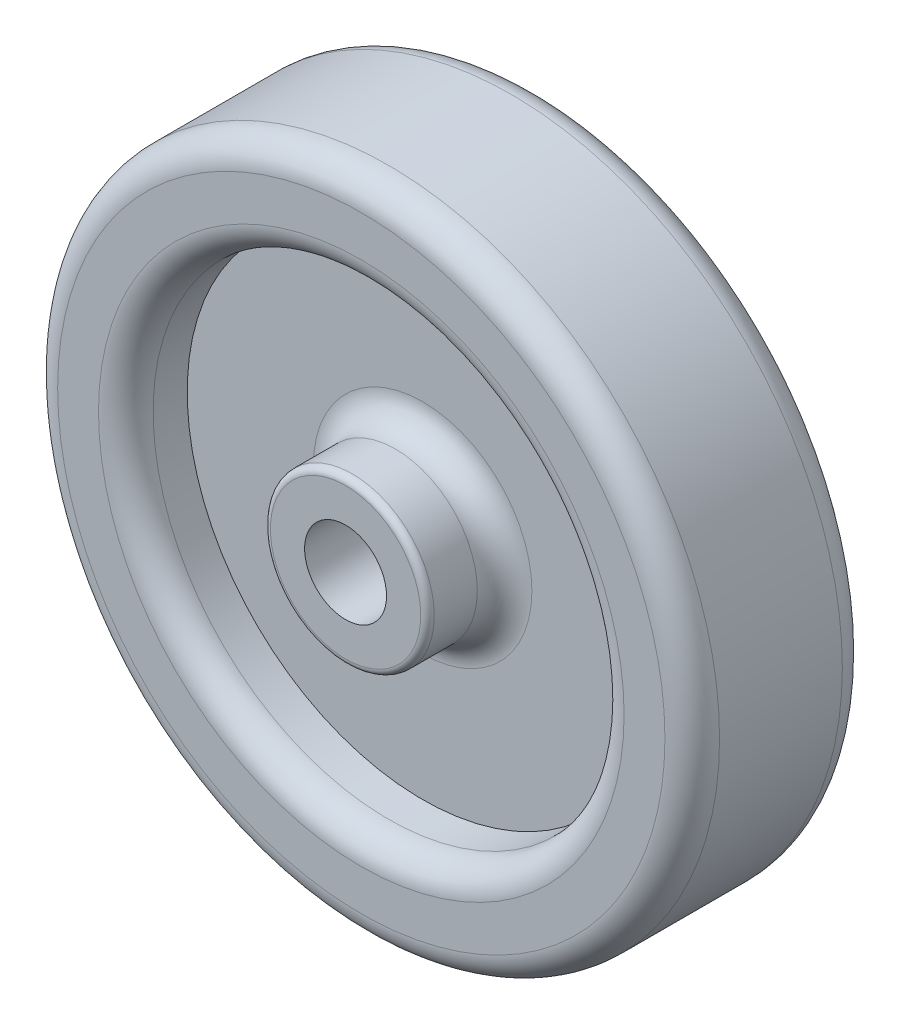
SolidWorks part; units mm, degrees
ref_plane "Front" through (0, 0, 0) normal (0, 0, 1) x (1, 0, 0)
ref_plane "Top" through (0, 0, 0) normal (0, 1, 0) x (1, 0, 0)
ref_plane "Right" through (0, 0, 0) normal (1, 0, 0) x (0, 0, -1)
sketch "Sketch1" plane through (0, 0, 0) normal (0, 0, 1) x (1, 0, 0)
  circle A0 centre (0, 0) radius 38.481
  circle A1 centre (0, 0) radius 4.7625
  dimension "D1" = 9.525
  dimension "D2" = 76.962
extrude "Boss-Extrude1" add sketch "Sketch1" against normal blind 10.3124 and the other way blind 10.3149
sketch "Sketch2" plane through (0, 0, 10.3149) normal (0, 0, 1) x (1, 0, 0)
  circle A0 centre (0, 0) radius 4.7625
  circle A1 centre (0, 0) radius 9.525
  dimension "D1" = 19.05
  dimension "D2" = 9.525
extrude "Boss-Extrude2" add sketch "Sketch2" along normal blind 1.8288 and the other way blind 22.4536
sketch "Sketch3" plane through (0, 0, -10.3124) normal (0, 0, -1) x (-1, 0, 0)
  circle A0 centre (0, 0) radius 9.525
  circle A1 centre (0, 0) radius 27.3812
  dimension "D1" = 54.7624
  dimension "D2" = 19.05
extrude "Cut-Extrude1" cut sketch "Sketch3" against normal blind 7.1374
sketch "Sketch4" plane through (0, 0, 10.3149) normal (0, 0, 1) x (1, 0, 0)
  circle A0 centre (0, 0) radius 9.525
  circle A1 centre (0, 0) radius 27.3812
  dimension "D1" = 19.05
  dimension "D2" = 54.7624
extrude "Cut-Extrude2" cut sketch "Sketch4" against normal blind 7.1374
fillet "Fillet1" radius 3.175 6 edges at (-9.525, 0, -3.175) (9.525, 0, 3.1775) (27.3812, 0, 10.3149) (-27.3812, 0, -10.3124) (38.481, 0, -10.3124) (38.481, 0, 10.3149)
fillet "Fillet2" radius 0.7874 2 edges at (9.525, 0, -12.1387) (9.525, 0, 12.1437)
